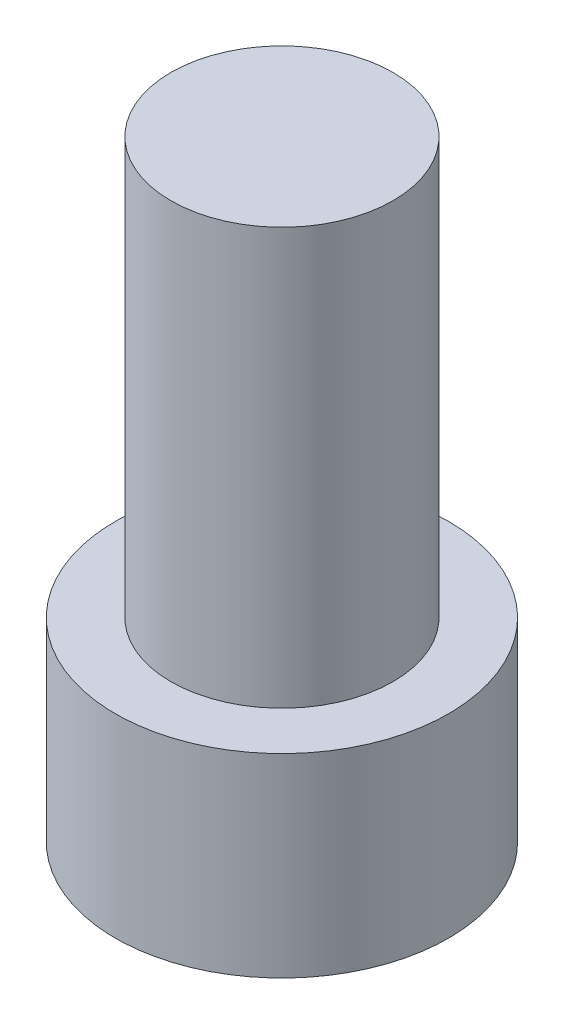
SolidWorks part; units mm, degrees
ref_plane "Front Plane" through (0, 0, 0) normal (0, 0, 1) x (1, 0, 0)
ref_plane "Top Plane" through (0, 0, 0) normal (0, 1, 0) x (1, 0, 0)
ref_plane "Right Plane" through (0, 0, 0) normal (1, 0, 0) x (0, 0, -1)
sketch "Sketch1" plane through (0, 0, 0) normal (0, 1, 0) x (1, 0, 0)
  circle A0 centre (0, 0) radius 4
  dimension "D1" = 8
extrude "Boss-Extrude1" add sketch "Sketch1" along normal blind 15
sketch "Sketch2" plane through (0, 0, 0) normal (0, -1, 0) x (1, 0, 0)
  circle A0 centre (0, 0) radius 6
  circle A1 centre (0, 0) radius 4
  circle A2 centre (0, 0) radius 4
  circle M3 centre (0, 0) radius 4
  dimension "D1" = 0
  dimension "D2" = 2
extrude "Boss-Extrude2" add sketch "Sketch2" along normal blind 2 separate body contours M3 | A0 M3
sketch "Sketch3" plane through (0, -2, 0) normal (0, -1, 0) x (1, 0, 0)
  line L1 (4.6188, 0) -> (2.3094, 4)
  line L2 (2.3094, 4) -> (-2.3094, 4)
  line L3 (-2.3094, 4) -> (-4.6188, 0)
  line L4 (-4.6188, 0) -> (-2.3094, -4)
  line L5 (-2.3094, -4) -> (2.3094, -4)
  line L6 (2.3094, -4) -> (4.6188, 0)
  circle A0 centre (0, 0) radius 4 construction
  circle A2 centre (0, 0) radius 6
  circle A3 centre (0, 0) radius 6
  point P1 (0, 0)
  point P10 (0, 0)
  dimension "D2" = 8
  dimension "D1" = 0
extrude "Boss-Extrude3" add sketch "Sketch3" along normal blind 5
